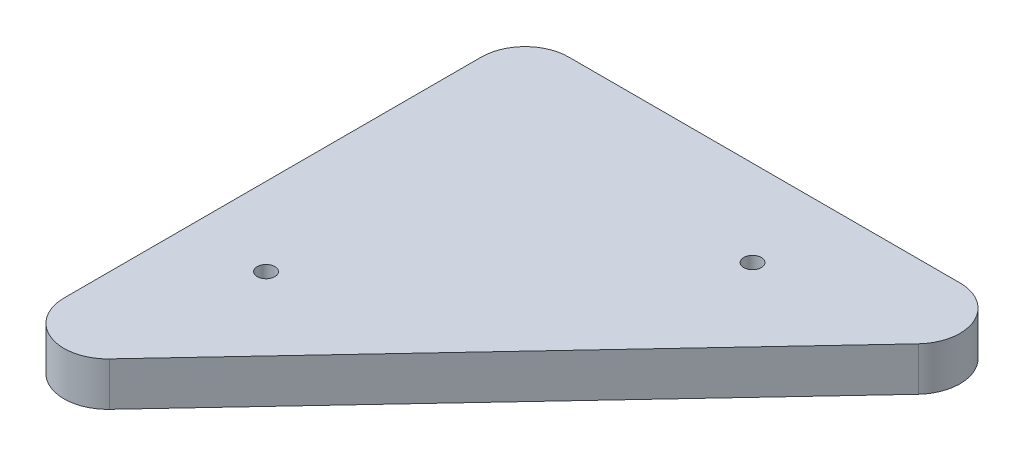
SolidWorks part; units mm, degrees
ref_plane "Front Plane" through (0, 0, 0) normal (0, 0, 1) x (1, 0, 0)
ref_plane "Top Plane" through (0, 0, 0) normal (0, 1, 0) x (1, 0, 0)
ref_plane "Right Plane" through (0, 0, 0) normal (1, 0, 0) x (0, 0, -1)
sketch "Sketch1" plane through (0, 0, 0) normal (0, 1, 0) x (1, 0, 0)
  line L0 (-12.7, 121.25) -> (-12.7, 0)
  line L1 (0, 133.95) -> (113.67, 133.95)
  line L2 (9.2652, -8.686) -> (122.9352, 112.564)
  arc A0 (-12.7, 0) -> (9.2652, -8.686) centre (0, 0) ccw
  arc A1 (0, 133.95) -> (-12.7, 121.25) centre (0, 121.25) ccw
  arc A2 (122.9352, 112.564) -> (113.67, 133.95) centre (113.67, 121.25) ccw
  dimension "D1" = 121.25
  dimension "D2" = 113.67
  dimension "D3" = 166.2
extrude "Boss-Extrude1" add sketch "Sketch1" along normal blind 12.7
hole_wizard "1/4-20 Tapped Hole1" positions "3DSketch1" profile "Sketch2" tap size "1/4-20" standard "ANSI Inch"
sketch3d "3DSketch1"
  line L0 (9.2652, 12.7, 8.686) -> (122.9352, 12.7, -112.564) construction
  arc A0 (-12.7, 12.7, 0) -> (9.2652, 12.7, 8.686) centre (0, 12.7, 0) ccw construction
  point P0 (10.0184, 12.7, -35.9813)
  point P2 (78.4119, 12.7, -108.9356)
  point P10 (0, 25.4, 0)
  dimension "D1" = 100
  dimension "D2" = 30
  dimension "D3" = 30
  dimension "D4" = 37.35
sketch "Sketch2" plane through (10.0184, 12.7, -35.9813) normal (1, 0, 0) x (0, 0, 1)
  line L0 (0, 0) -> (0, 20.5838)
  line L1 (0, 20.5838) -> (2.5527, 19.05)
  line L2 (2.5527, 19.05) -> (2.5527, 0)
  line L5 (2.5527, 0) -> (0, 0)
  line L10 (0, 20.5838) -> (-2.5527, 19.05) construction
  line L11 (0, -6.35) -> (0, 107.95) construction
  dimension "Tap Drill Dia." = 5.1054
  dimension "Tap Drill Depth" = 19.05
  dimension "Drill Angle" = 118
cosmetic thread "Hole Thread1" parameters "D1"=12.7, "D2"=6.35
cosmetic thread "Hole Thread2" parameters "D1"=12.7, "D2"=6.35
